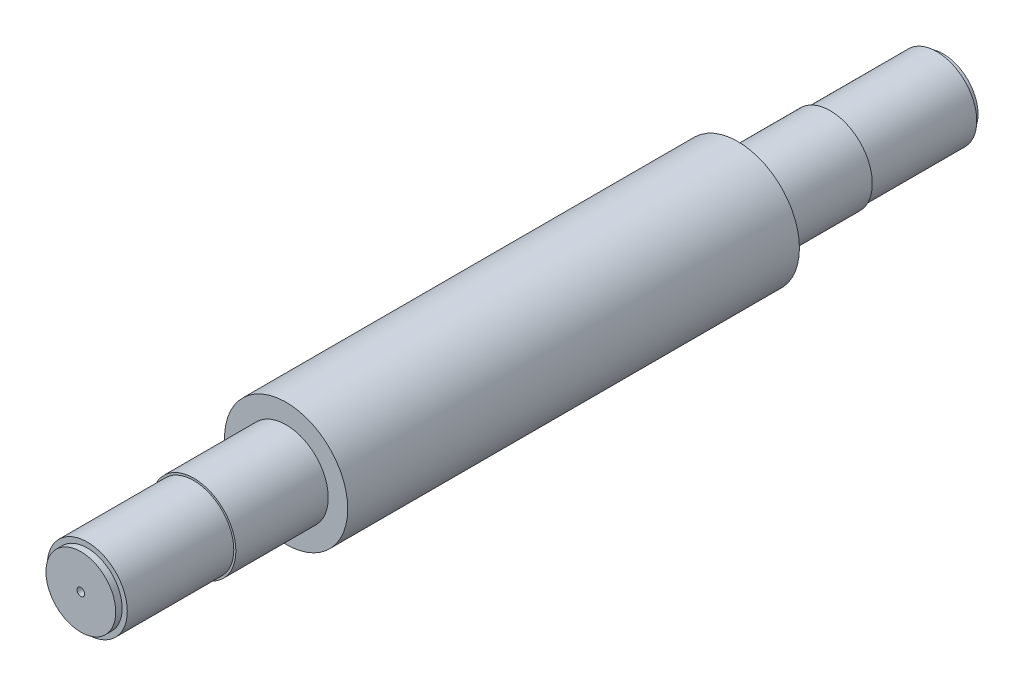
SolidWorks part; units mm, degrees
ref_plane "Front Plane" through (0, 0, 0) normal (0, 0, 1) x (1, 0, 0)
ref_plane "Top Plane" through (0, 0, 0) normal (0, 1, 0) x (1, 0, 0)
ref_plane "Right Plane" through (0, 0, 0) normal (1, 0, 0) x (0, 0, -1)
sketch "Sketch1" plane through (0, 0, 0) normal (0, 0, 1) x (1, 0, 0)
  circle A0 centre (0, 0) radius 60
  dimension "D1" = 120
extrude "Boss-Extrude1" add sketch "Sketch1" along normal blind 440
sketch "Sketch2" plane through (0, 0, 0) normal (0, 0, -1) x (-1, 0, 0)
  circle A0 centre (0, 0) radius 41
  dimension "D1" = 82
extrude "Boss-Extrude2" add sketch "Sketch2" along normal blind 90
sketch "Sketch3" plane through (0, 0, 440) normal (0, 0, 1) x (1, 0, 0)
  circle A0 centre (0, 0) radius 41
  dimension "D1" = 82
extrude "Boss-Extrude3" add sketch "Sketch3" along normal blind 90
sketch "Sketch4" plane through (0, 0, 530) normal (0, 0, 1) x (1, 0, 0)
  circle A0 centre (0, 0) radius 39
  dimension "D1" = 78
extrude "Boss-Extrude4" add sketch "Sketch4" along normal blind 103.75
sketch "Sketch5" plane through (0, 0, -90) normal (0, 0, -1) x (-1, 0, 0)
  circle A0 centre (0, 0) radius 39
  dimension "D1" = 78
extrude "Boss-Extrude5" add sketch "Sketch5" along normal blind 103.75
sketch "Sketch6" plane through (0, 0, -193.75) normal (0, 0, -1) x (-1, 0, 0)
  circle A0 centre (0, 0) radius 34
  dimension "D1" = 68
extrude "Boss-Extrude6" add sketch "Sketch6" along normal blind 6.25
sketch "Sketch7" plane through (0, 0, 633.75) normal (0, 0, 1) x (1, 0, 0)
  circle A0 centre (0, 0) radius 34
  dimension "D1" = 68
extrude "Boss-Extrude7" add sketch "Sketch7" along normal blind 6.25
sketch "Sketch8" plane through (0, 0, 640) normal (0, 0, 1) x (1, 0, 0)
  circle A0 centre (0, 0) radius 3.75
  dimension "D1" = 7.5
extrude "Cut-Extrude1" cut sketch "Sketch8" against normal blind 840
